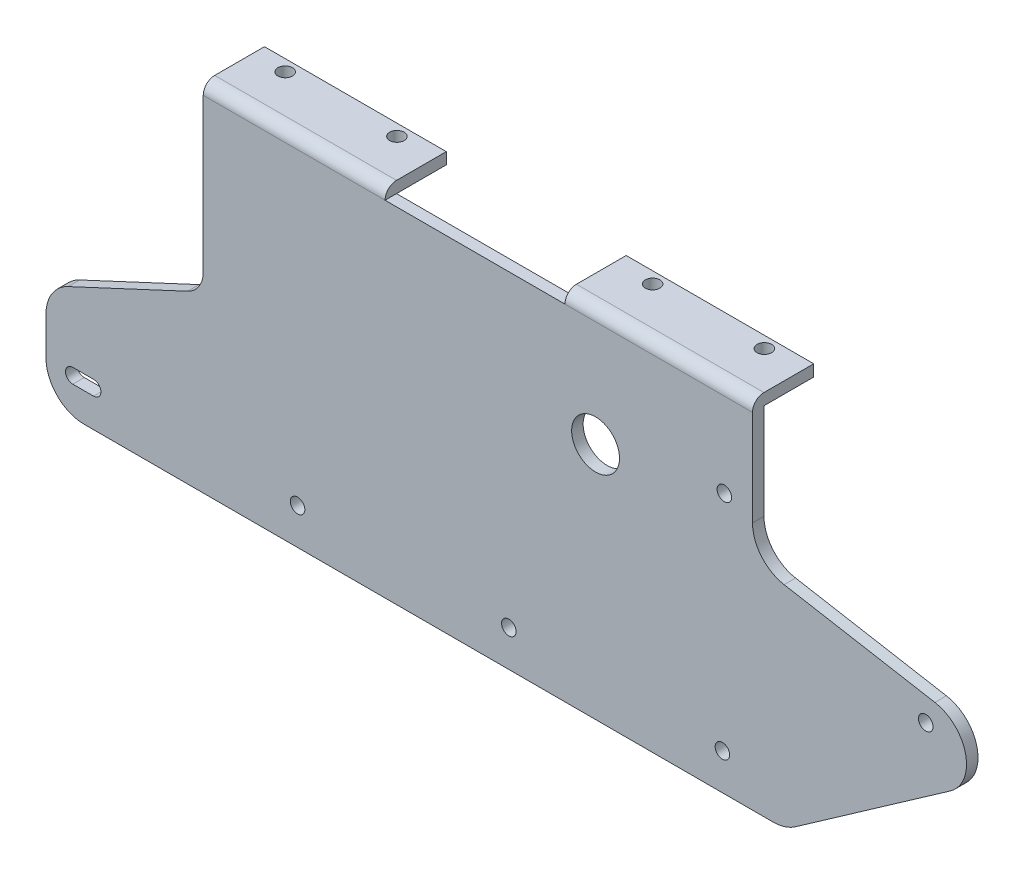
SolidWorks part; units mm, degrees
material "1060 Alloy"
ref_plane "Front Plane" through (0, 0, 0) normal (0, 0, 1) x (1, 0, 0)
ref_plane "Top Plane" through (0, 0, 0) normal (0, 1, 0) x (1, 0, 0)
ref_plane "Right Plane" through (0, 0, 0) normal (1, 0, 0) x (0, 0, -1)
sketch "Sketch1" plane through (0, 0, 0) normal (0, 0, 1) x (1, 0, 0)
  line L0 (0, 0) -> (143.5, 0)
  line L1 (143.5, 0) -> (143.5, -25)
  line L2 (151.7635, -34.8481) -> (191.1558, -41.794)
  line L3 (195.1551, -59.8336) -> (154.6558, -88.1915)
  line L4 (148.92, -90) -> (-31.08, -90)
  line L5 (-41.08, -80) -> (-41.08, -70)
  line L6 (-35.3061, -60.9369) -> (-4.0543, -46.3639)
  line L7 (0, 0) -> (0, -40)
  arc A0 (-41.08, -70) -> (-35.3061, -60.9369) centre (-31.08, -70) cw
  arc A1 (143.5, -25) -> (151.7635, -34.8481) centre (153.5, -25) ccw
  arc A2 (191.1558, -41.794) -> (195.1551, -59.8336) centre (189.4193, -51.6421) cw
  arc A3 (148.92, -90) -> (154.6558, -88.1915) centre (148.92, -80) ccw
  arc A4 (-41.08, -80) -> (-31.08, -90) centre (-31.08, -80) ccw
  arc A5 (-4.0543, -46.3639) -> (0, -40) centre (-7.0218, -40) ccw
  dimension "D6" = 10
  dimension "D7" = 10
  dimension "D10" = 10
  dimension "D11" = 40
  dimension "D12" = 10
  dimension "D15" = 10
  dimension "D1" = 143.5
  dimension "D2" = 25
  dimension "D3" = 40
  dimension "D4" = 90
  dimension "D5" = 10
  dimension "D8" = 180
  dimension "D9" = 35
  dimension "D13" = 10
  dimension "D14" = 25
extrude "Boss-Extrude1" add sketch "Sketch1" along normal blind 3
sketch "Sketch2" plane through (0, 0, 3) normal (0, 0, 1) x (1, 0, 0)
  line L3 (154.6558, -88.1915) -> (195.1551, -59.8336) construction
  line L4 (135.6404, -80.5) -> (135.6404, -90) construction
  line L5 (-31.08, -90) -> (148.92, -90) construction
  line L6 (135.6404, -80.5) -> (165.6404, -80.5) construction
  line L7 (135.6404, -80.5) -> (79.8404, -80.5) construction
  line L9 (24.6404, -80.5) -> (-28.6346, -80.5) construction
  line L10 (-28.6346, -80.5) -> (-34.0846, -80.5) construction
  line L11 (-28.6346, -82.4) -> (-34.0846, -82.4)
  line L12 (-28.6346, -78.6) -> (-34.0846, -78.6)
  line L13 (102.5, -27.75) -> (0, -27.75) construction
  line L14 (0, 0) -> (0, -40) construction
  line L15 (143.5, 0) -> (0, 0) construction
  circle A0 centre (188.7586, -47.5651) radius 1.9
  circle A2 centre (135.6404, -80.5) radius 1.9
  circle A3 centre (79.8404, -80.5) radius 1.9
  circle A4 centre (24.6404, -80.5) radius 1.9
  arc A5 (-28.6346, -82.4) -> (-28.6346, -78.6) centre (-28.6346, -80.5) ccw
  arc A6 (-34.0846, -78.6) -> (-34.0846, -82.4) centre (-34.0846, -80.5) ccw
  circle A7 centre (102.5, -27.75) radius 6.25
  circle A8 centre (136.1404, -22) radius 1.9
  point P3 (141.9811, -22)
  point P4 (137.9556, -22)
  point P5 (0, 0)
  point P6 (0, 0)
  point P22 (-31.3596, -80.5)
  point P37 (143.5, -22)
  dimension "D1" = 3.8
  dimension "D7" = 1.9
  dimension "D8" = 5.45
  dimension "D11" = 12.5
  dimension "D2" = 62.5
  dimension "D3" = 9.5
  dimension "D4" = 30
  dimension "D5" = 55.8
  dimension "D6" = 167
  dimension "D9" = 102.5
  dimension "D10" = 27.75
  dimension "D12" = 58.5
  dimension "D13" = 68
  dimension "D14" = 111
  dimension "D15" = 0.5
extrude "Cut-Extrude1" cut sketch "Sketch2" against normal through all contours A7 | A2 | A0 | A3 | A4 | L12 A6 L11 A5 | A8
sketch "Sketch3" plane through (143.5, 0, 0) normal (1, 0, 0) x (0, 0, -1)
  line L0 (0, 0) -> (13, 0)
  line L1 (0, 3) -> (13, 3)
  line L2 (13, 3) -> (13, 0)
  line L3 (-3, 0) -> (0, 0)
  line L4 (-3, -25) -> (-3, 0) construction
  line L5 (-3, -25) -> (-3, 0)
  line L6 (0, -25) -> (0, 0) construction
  line L7 (0, -25) -> (0, 0)
  arc A0 (0, 3) -> (-3, 0) centre (0, 0) ccw
  dimension "D1" = 3
  dimension "D2" = 16
extrude "Boss-Extrude2" add sketch "Sketch3" against normal up to surface (143.5 mm away) contours L0 L2 L1 A0 L3 up to face at (0, -20, 1.5)
sketch "Sketch4" plane through (0, 3, 0) normal (0, 1, 0) x (1, 0, 0)
  line L0 (47.5, 13) -> (47.5, -3)
  line L1 (0, 13) -> (143.5, 13) construction
  line L2 (143.5, -3) -> (0, -3) construction
  line L3 (47.5, -3) -> (94.5, -3)
  line L4 (94.5, -3) -> (94.5, 13)
  line L5 (94.5, 13) -> (47.5, 13)
  line L6 (0, 13) -> (0, 0) construction
  line L7 (143.5, 0) -> (143.5, 13) construction
  dimension "D1" = 47.5
  dimension "D2" = 49
extrude "Cut-Extrude2" cut sketch "Sketch4" against normal up to vertex (3 mm away) contours L5 L0 L3 L4
sketch "Sketch5" plane through (0, 3, 0) normal (0, 1, 0) x (1, 0, 0)
  line L0 (0, 10) -> (143.5, 10) construction
  line L1 (0, 13) -> (0, 0) construction
  line L2 (143.5, 0) -> (143.5, 13) construction
  line L3 (0, 13) -> (47.5, 13) construction
  line L4 (47.5, 13) -> (47.5, 0) construction
  line L5 (94.5, 0) -> (94.5, 13) construction
  circle A0 centre (8.4, 10) radius 1.9
  circle A1 centre (37.6, 10) radius 1.9
  circle A2 centre (104.4, 10) radius 1.9
  circle A3 centre (133.6, 10) radius 1.9
  dimension "D2" = 3.8
  dimension "D1" = 3
  dimension "D3" = 8.4
  dimension "D4" = 9.9
  dimension "D5" = 9.9
  dimension "D6" = 9.9
extrude "Cut-Extrude3" cut sketch "Sketch5" against normal through all contours A0 | A1 | A2 | A3
